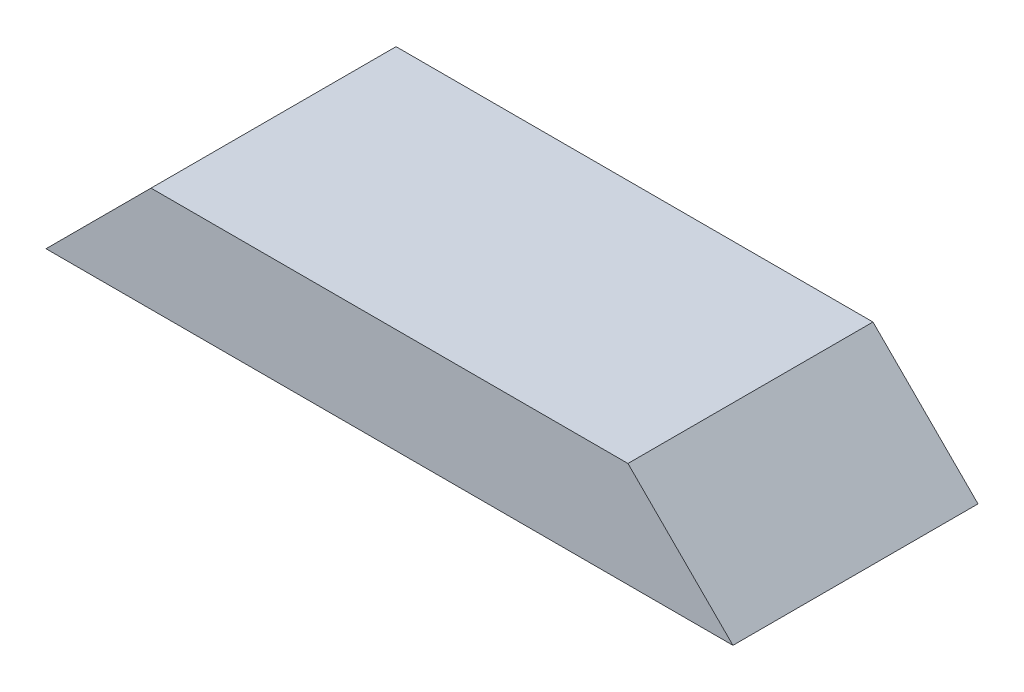
SolidWorks part; units mm, degrees
ref_plane "Front Plane" through (0, 0, 0) normal (0, 0, 1) x (1, 0, 0)
ref_plane "Top Plane" through (0, 0, 0) normal (0, 1, 0) x (1, 0, 0)
ref_plane "Right Plane" through (0, 0, 0) normal (1, 0, 0) x (0, 0, -1)
sketch "Sketch1" plane through (0, 0, 0) normal (0, 1, 0) x (1, 0, 0)
  line L1 (0, 0) -> (249.2375, 0)
  line L2 (0, 0) -> (0, 88.9)
  line L3 (0, 88.9) -> (249.2375, 88.9)
  line L4 (249.2375, 0) -> (249.2375, 88.9)
  dimension "D1" = 88.9
  dimension "D2" = 249.2375
extrude "Boss-Extrude1" add sketch "Sketch1" along normal blind 38.1
sketch "Sketch2" plane through (0, 0, 0) normal (0, 0, 1) x (1, 0, 0)
  line L0 (0, 0) -> (38.1, 38.1)
  line L1 (0, 38.1) -> (249.2375, 38.1) construction
  line L2 (38.1, 38.1) -> (0, 38.1)
  line L3 (0, 38.1) -> (0, 0)
  line L5 (249.2375, 0) -> (249.2375, 38.1)
  line L9 (249.2375, 38.1) -> (211.1375, 38.1)
  line L10 (211.1375, 38.1) -> (249.2375, 0)
  dimension "D1" = 38.1
  dimension "D2" = 38.1
  dimension "D3" = 38.1
extrude "Cut-Extrude1" cut sketch "Sketch2" against normal through all
